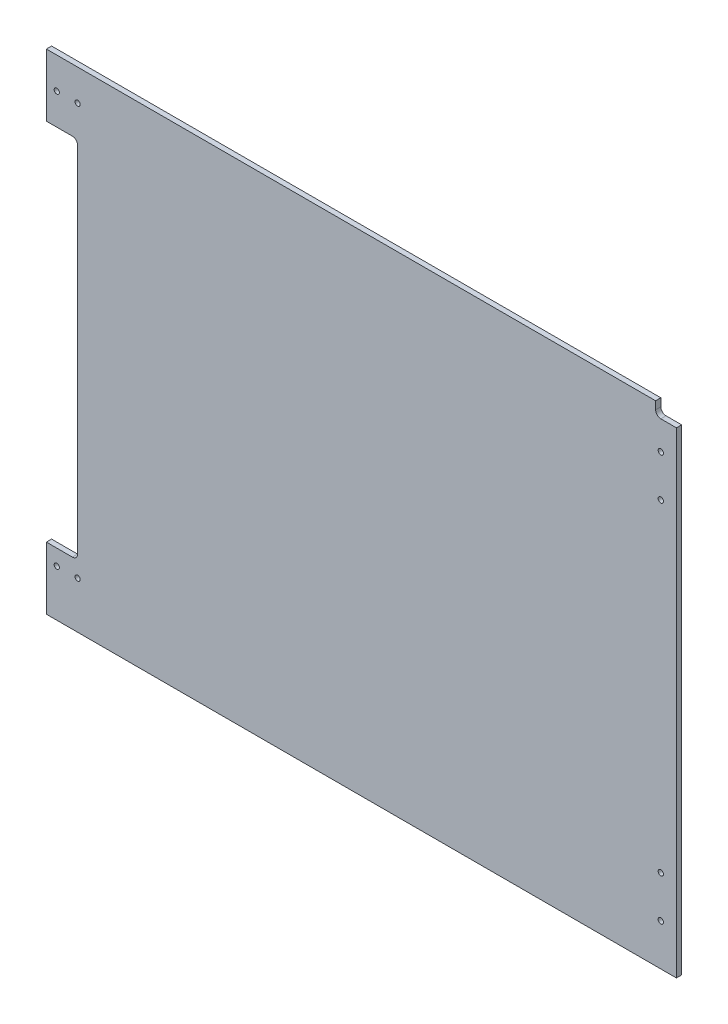
SolidWorks part; units mm, degrees
material "PC High Viscosity"
ref_plane "Front Plane" through (0, 0, 0) normal (0, 0, 1) x (1, 0, 0)
ref_plane "Top Plane" through (0, 0, 0) normal (0, 1, 0) x (1, 0, 0)
ref_plane "Right Plane" through (0, 0, 0) normal (1, 0, 0) x (0, 0, -1)
sketch "Sketch1" plane through (0, 0, 0) normal (0, 0, 1) x (1, 0, 0)
  line L1 (-368.3, -298.45) -> (368.3, -298.45)
  line L2 (-368.3, -298.45) -> (-368.3, 298.45)
  line L3 (-368.3, 298.45) -> (368.3, 298.45)
  line L4 (368.3, -298.45) -> (368.3, 298.45)
  line L5 (-368.3, -298.45) -> (368.3, 298.45) construction
  line L6 (-368.3, 298.45) -> (368.3, -298.45) construction
  point P0 (0, 0)
  dimension "D1" = 596.9
  dimension "D2" = 736.6
extrude "Boss-Extrude1" add sketch "Sketch1" along normal blind 6.35
sketch "Sketch2" plane through (0, 0, 6.35) normal (0, 0, 1) x (1, 0, 0)
  line L0 (-368.3, 285.75) -> (368.3, 285.75) construction
  line L1 (-368.3, 298.45) -> (-368.3, -298.45) construction
  line L2 (368.3, -298.45) -> (368.3, 298.45) construction
  line L3 (-368.3, 0) -> (368.3, 0) construction
  line L4 (368.3, 298.45) -> (-368.3, 298.45) construction
  line L5 (-368.3, -285.75) -> (368.3, -285.75) construction
  line L6 (-355.6, 298.45) -> (-355.6, -298.45) construction
  line L7 (-368.3, -298.45) -> (368.3, -298.45) construction
  line L8 (0, 298.45) -> (0, -298.45) construction
  point P8 (-336.55, 285.75)
  point P9 (336.55, 285.75)
  point P15 (336.55, -285.75)
  point P16 (-336.55, -285.75)
  point P23 (-355.6, 250.825)
  point P24 (355.6, 250.825)
  point P25 (355.6, -250.825)
  point P26 (-355.6, -250.825)
  dimension "D1" = 12.7
  dimension "D2" = 31.75
  dimension "D3" = 31.75
  dimension "D4" = 12.7
  dimension "D5" = 47.625
hole_wizard "1/4 (0.25) Diameter Hole1" positions "Sketch3" profile "Sketch4" hole size "1/4" standard "ANSI Inch"
sketch "Sketch3" plane through (0, 0, 6.35) normal (0, 0, 1) x (1, 0, 0)
  point P0 (-336.55, 290.5125)
  point P3 (336.55, 290.5125)
  point P16 (-355.6, 255.5875)
  point P20 (355.6, 255.5875)
  point P24 (-355.6, -255.5875)
  point P27 (355.6, -255.5875)
  point P30 (336.55, -290.5125)
  point P33 (-336.55, -290.5125)
sketch "Sketch4" plane through (-336.55, 290.5125, 6.35) normal (1, 0, 0) x (0, -1, 0)
  line L0 (0, 0) -> (0, 6.35)
  line L1 (0, 6.35) -> (3.175, 6.35)
  line L2 (3.175, 6.35) -> (3.175, 0)
  line L5 (3.175, 0) -> (0, 0)
  line L11 (0, -6.35) -> (0, 107.95) construction
  dimension "Thru Hole Dia." = 6.35
  dimension "Thru Hole Depth" = 6.35
sketch "Sketch5" plane through (0, 0, 6.35) normal (0, 0, 1) x (1, 0, 0)
  line L1 (-368.3, 298.45) -> (-400.05, 298.45)
  line L2 (-368.3, 298.45) -> (-368.3, 222.25)
  line L3 (-368.3, 222.25) -> (-400.05, 222.25)
  line L4 (-400.05, 298.45) -> (-400.05, 222.25)
  line L5 (-368.3, -298.45) -> (-400.05, -298.45)
  line L6 (-368.3, -298.45) -> (-368.3, -222.25)
  line L7 (-368.3, -222.25) -> (-400.05, -222.25)
  line L8 (-400.05, -298.45) -> (-400.05, -222.25)
  dimension "D1" = 31.75
  dimension "D2" = 76.2
  dimension "D3" = 76.2
extrude "Boss-Extrude2" add sketch "Sketch5" against normal up to surface (6.35 mm away)
sketch "Sketch6" plane through (0, 0, 6.35) normal (0, 0, 1) x (1, 0, 0)
  line L0 (-368.3, -222.25) -> (-400.05, -222.25) construction
  line L1 (-368.3, 222.25) -> (-361.95, 222.25)
  line L2 (-368.3, 222.25) -> (-368.3, -222.25)
  line L3 (-368.3, -222.25) -> (-361.95, -222.25)
  line L4 (-361.95, 222.25) -> (-361.95, -222.25)
  dimension "D1" = 6.35
extrude "Cut-Extrude1" cut sketch "Sketch6" against normal through all
fillet "Fillet1" radius 6.35
sketch "Sketch7" plane through (0, 0, 6.35) normal (0, 0, 1) x (1, 0, 0)
  line L0 (349.25, 298.45) -> (349.25, -298.45) construction
  line L1 (368.3, 298.45) -> (-400.05, 298.45) construction
  line L2 (-400.05, -298.45) -> (368.3, -298.45) construction
  line L3 (368.3, -298.45) -> (368.3, 298.45) construction
  line L4 (349.25, 0) -> (-361.95, 0) construction
  line L5 (-361.95, -215.9) -> (-361.95, 215.9) construction
  point P8 (349.25, 247.65)
  point P9 (349.25, 196.85)
  point P14 (349.25, -247.65)
  point P15 (349.25, -196.85)
  dimension "D1" = 19.05
  dimension "D2" = 50.8
  dimension "D3" = 50.8
hole_wizard "F (0.257) Diameter Hole1" positions "Sketch8" profile "Sketch9" hole size "F" standard "ANSI Inch"
sketch "Sketch8" plane through (0, 0, 6.35) normal (0, 0, 1) x (1, 0, 0)
  point P0 (349.25, 247.65)
  point P3 (349.25, 196.85)
  point P6 (349.25, -196.85)
  point P9 (349.25, -247.65)
sketch "Sketch9" plane through (349.25, 247.65, 6.35) normal (1, 0, 0) x (0, -1, 0)
  line L0 (0, 0) -> (0, 6.35)
  line L1 (0, 6.35) -> (3.2639, 6.35)
  line L2 (3.2639, 6.35) -> (3.2639, 0)
  line L5 (3.2639, 0) -> (0, 0)
  line L11 (0, -6.35) -> (0, 107.95) construction
  dimension "Thru Hole Dia." = 6.5278
  dimension "Thru Hole Depth" = 6.35
sketch "Sketch10" plane through (0, 0, 6.35) normal (0, 0, 1) x (1, 0, 0)
  line L0 (-400.05, 260.35) -> (-361.95, 260.35) construction
  line L1 (-400.05, 298.45) -> (-400.05, 222.25) construction
  line L2 (-361.95, 0) -> (349.25, 0) construction
  line L3 (349.25, 298.45) -> (349.25, -298.45) construction
  line L4 (-400.05, -241.3) -> (-361.95, -241.3) construction
  line L6 (-400.05, -298.45) -> (368.3, -298.45) construction
  line L7 (-400.05, -222.25) -> (-400.05, -298.45) construction
  point P4 (-387.35, 260.35)
  point P6 (-361.95, 260.35)
  point P13 (-387.35, -241.3)
  dimension "D1" = 12.7
  dimension "D2" = 38.1
  dimension "D3" = 57.15
  dimension "D4" = 12.7
  dimension "D5" = 38.1
hole_wizard "1/4 (0.25) Diameter Hole2" positions "Sketch11" profile "Sketch12" hole size "1/4" standard "ANSI Inch"
sketch "Sketch11" plane through (0, 0, 6.35) normal (0, 0, 1) x (1, 0, 0)
  point P0 (-387.35, 260.35)
  point P3 (-361.95, 260.35)
  point P6 (-361.95, -241.3)
  point P9 (-387.35, -241.3)
sketch "Sketch12" plane through (-387.35, 260.35, 6.35) normal (1, 0, 0) x (0, -1, 0)
  line L0 (0, 0) -> (0, 8.2567)
  line L1 (0, 8.2567) -> (3.175, 6.349)
  line L2 (3.175, 6.349) -> (3.175, 0)
  line L5 (3.175, 0) -> (0, 0)
  line L10 (0, 8.2567) -> (-3.175, 6.349) construction
  line L11 (0, -6.35) -> (0, 107.95) construction
  dimension "Hole Dia." = 6.35
  dimension "Hole Depth" = 6.349
  dimension "Drill Angle" = 118
sketch "Sketch13" plane through (0, 0, 6.35) normal (0, 0, 1) x (1, 0, 0)
  line L1 (368.3, 298.45) -> (342.9, 298.45)
  line L2 (368.3, 298.45) -> (368.3, 282.575)
  line L3 (368.3, 282.575) -> (349.25, 282.575)
  line L4 (342.9, 298.45) -> (342.9, 288.925)
  arc A0 (349.25, 282.575) -> (342.9, 288.925) centre (349.25, 288.925) cw
  point P7 (342.9, 282.575)
  dimension "D3" = 6.35
  dimension "D1" = 25.4
  dimension "D2" = 15.875
extrude "Cut-Extrude2" cut sketch "Sketch13" against normal through all
equation "\"D3@Sketch2\"=\"D2@Sketch2\""
